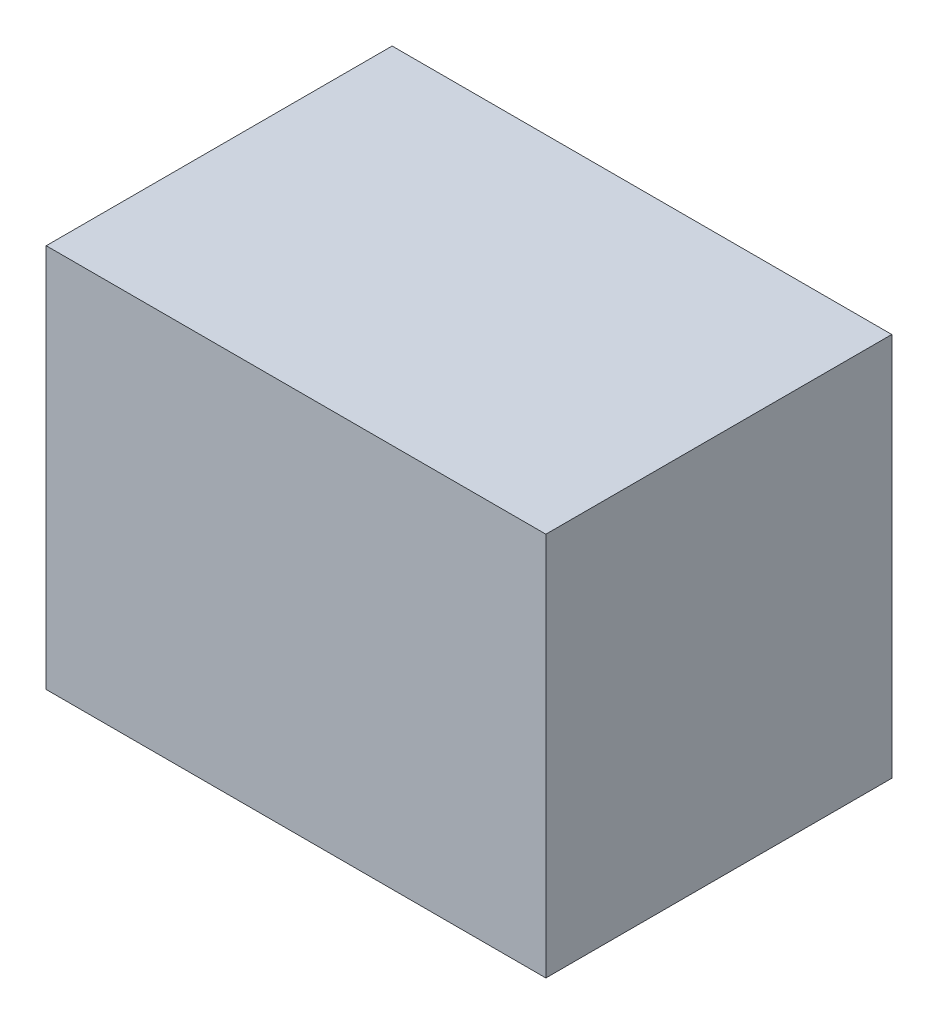
SolidWorks part; units mm, degrees
ref_plane "前视基准面" through (0, 0, 0) normal (0, 0, 1) x (1, 0, 0)
ref_plane "上视基准面" through (0, 0, 0) normal (0, 1, 0) x (1, 0, 0)
ref_plane "右视基准面" through (0, 0, 0) normal (1, 0, 0) x (0, 0, -1)
sketch "草图1" plane through (0, 0, 0) normal (0, 1, 0) x (1, 0, 0)
  line L1 (-65, 45) -> (65, 45)
  line L2 (-65, 45) -> (-65, -45)
  line L3 (-65, -45) -> (65, -45)
  line L4 (65, 45) -> (65, -45)
  line L5 (-65, 45) -> (65, -45) construction
  line L6 (-65, -45) -> (65, 45) construction
  point P0 (0, 0)
  dimension "D1" = 90
  dimension "D2" = 130
extrude "凸台-拉伸1" add sketch "草图1" along normal blind 100
